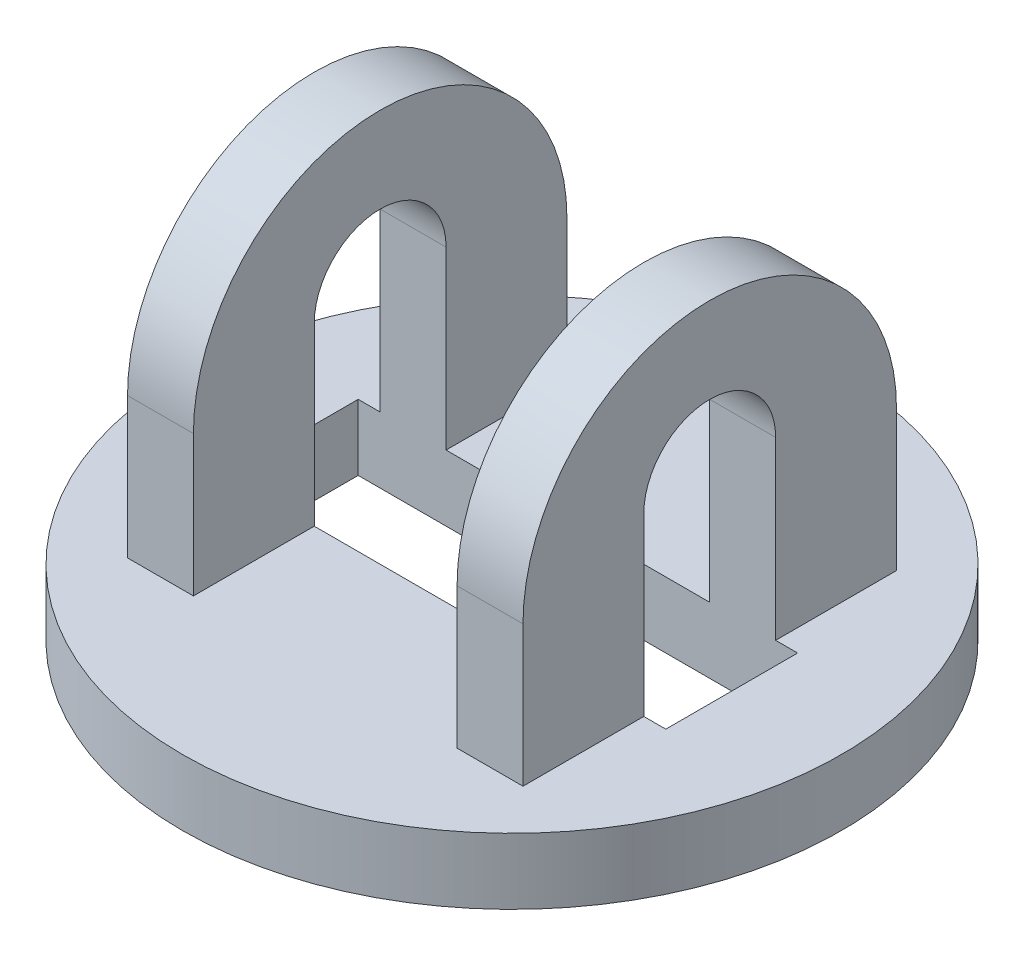
SolidWorks part; units mm, degrees
ref_plane "Front Plane" through (0, 0, 0) normal (0, 0, 1) x (1, 0, 0)
ref_plane "Top Plane" through (0, 0, 0) normal (0, 1, 0) x (1, 0, 0)
ref_plane "Right Plane" through (0, 0, 0) normal (1, 0, 0) x (0, 0, -1)
sketch "Sketch1" plane through (0, 0, 0) normal (0, 1, 0) x (1, 0, 0)
  circle A0 centre (0, 0) radius 15
  dimension "D1" = 30
extrude "Boss-Extrude1" add sketch "Sketch1" along normal blind 3
sketch "Sketch2" plane through (0, 3, 0) normal (0, 1, 0) x (1, 0, 0)
  line L0 (-7.5, 0) -> (7.5, 0) construction
  line L2 (-9, 8.5) -> (-6, 8.5)
  line L3 (-9, 8.5) -> (-9, -8.5)
  line L4 (-9, -8.5) -> (-6, -8.5)
  line L5 (-6, 8.5) -> (-6, -8.5)
  line L6 (-9, 8.5) -> (-6, -8.5) construction
  line L7 (-9, -8.5) -> (-6, 8.5) construction
  line L8 (6, 8.5) -> (9, 8.5)
  line L9 (6, 8.5) -> (6, -8.5)
  line L10 (6, -8.5) -> (9, -8.5)
  line L11 (9, 8.5) -> (9, -8.5)
  line L12 (6, 8.5) -> (9, -8.5) construction
  line L13 (6, -8.5) -> (9, 8.5) construction
  point P4 (0, 0)
  dimension "D1" = 15
  dimension "D2" = 17
  dimension "D3" = 3
extrude "Boss-Extrude2" add sketch "Sketch2" along normal blind 15
sketch "Sketch3" plane through (-9, 0, 0) normal (-1, 0, 0) x (0, 0, 1)
  line L0 (-8.5, 9.4) -> (8.5, 9.4) construction
  line L1 (-8.5, 18) -> (-8.5, 3) construction
  line L2 (8.5, 18) -> (8.5, 3) construction
  line L3 (15, 3) -> (-15, 3) construction
  line L4 (-8.5, 9.4) -> (-8.5, 18)
  line L5 (-8.5, 18) -> (8.5, 18)
  line L6 (8.5, 18) -> (8.5, 9.4)
  arc A0 (-8.5, 9.4) -> (8.5, 9.4) centre (0, 9.4) cw
  dimension "D1" = 6.4
extrude "Cut-Extrude1" cut sketch "Sketch3" against normal through all
sketch "Sketch4" plane through (0, 0, 0) normal (0, -1, 0) x (-1, 0, 0)
  line L1 (-10, -3) -> (10, -3)
  line L2 (-10, -3) -> (-10, 3)
  line L3 (-10, 3) -> (10, 3)
  line L4 (10, -3) -> (10, 3)
  line L5 (-10, -3) -> (10, 3) construction
  line L6 (-10, 3) -> (10, -3) construction
  point P0 (0, 0)
  dimension "D1" = 20
  dimension "D2" = 6
extrude "Cut-Extrude2" cut sketch "Sketch4" against normal blind 11
sketch "Sketch5" plane through (-9, 0, 0) normal (-1, 0, 0) x (0, 0, 1)
  line L0 (3, 11) -> (-3, 11)
  arc A0 (3, 11) -> (-3, 11) centre (0, 11) ccw
extrude "Cut-Extrude3" cut sketch "Sketch5" against normal through all
